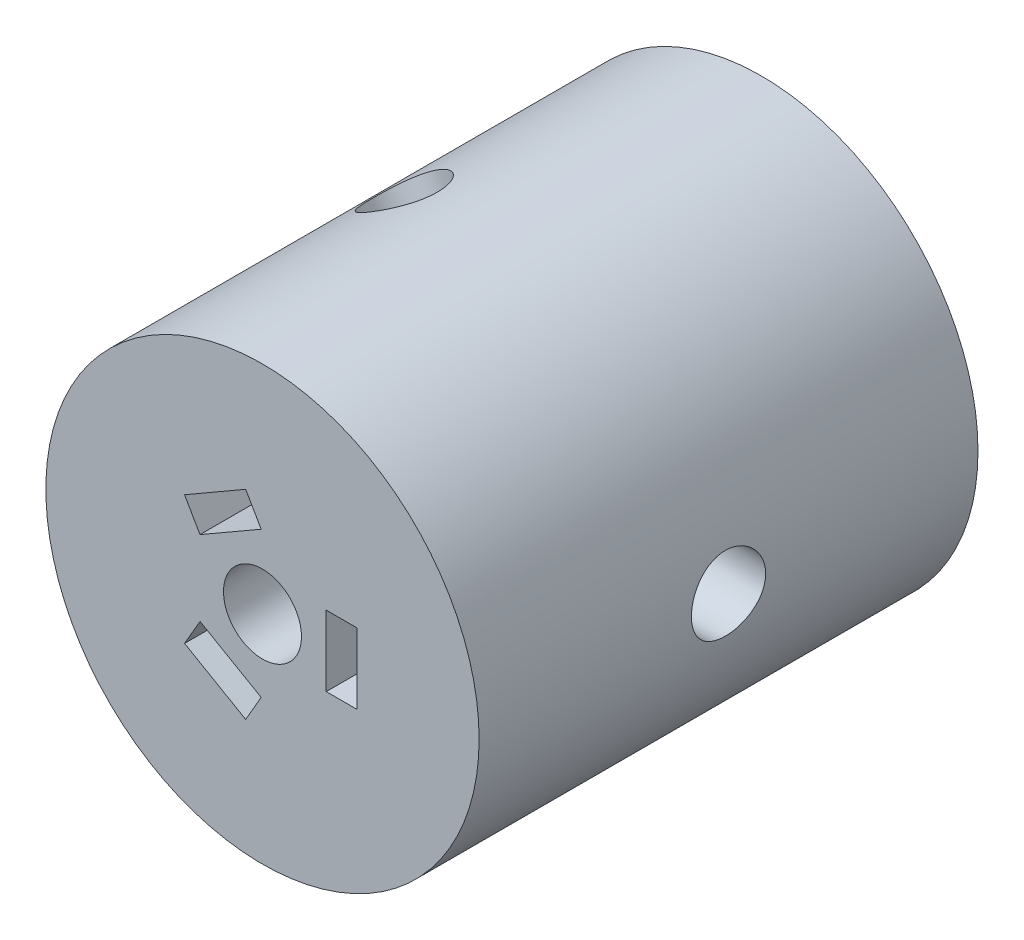
SolidWorks part; units mm, degrees
ref_plane "Front" through (0, 0, 0) normal (0, 0, 1) x (1, 0, 0)
ref_plane "Top" through (0, 0, 0) normal (0, 1, 0) x (1, 0, 0)
ref_plane "Right" through (0, 0, 0) normal (1, 0, 0) x (0, 0, -1)
sketch "Sketch1" plane through (0, 0, 0) normal (0, 0, 1) x (1, 0, 0)
  circle A0 centre (0, 0) radius 17.5
  circle A1 centre (0, 0) radius 3.15
  dimension "D1" = 35
  dimension "D2" = 6.3
extrude "Boss-Extrude1" add sketch "Sketch1" along normal blind 40.3
sketch "Sketch2" plane through (0, 0, 40.3) normal (0, 0, 1) x (1, 0, 0)
  line L3 (7.65, 0) -> (7.65, 2.85)
  line L5 (7.65, 0) -> (7.65, -2.85)
  line L7 (7.65, 2.85) -> (5.15, 2.85)
  line L8 (5.15, 2.85) -> (5.15, -2.85)
  line L9 (5.15, -2.85) -> (7.65, -2.85)
  line L16 (-3.825, -6.6251) -> (-1.3568, -8.0501)
  line L17 (-3.825, -6.6251) -> (-6.2932, -5.2001)
  line L18 (-1.3568, -8.0501) -> (-0.1068, -5.885)
  line L19 (-0.1068, -5.885) -> (-5.0432, -3.035)
  line L20 (-5.0432, -3.035) -> (-6.2932, -5.2001)
  line L21 (-3.825, 6.6251) -> (-6.2932, 5.2001)
  line L22 (-3.825, 6.6251) -> (-1.3568, 8.0501)
  line L23 (-1.3568, 8.0501) -> (-0.1054, 5.8826)
  line L24 (-0.1054, 5.8826) -> (-5.0482, 3.0353)
  line L25 (-5.0482, 3.0353) -> (-6.2932, 5.2001)
  dimension "D5" = 2.85
  dimension "D6" = 2.85
  dimension "D7" = 2.85
  dimension "D8" = 2.85
  dimension "D9" = 2.5
  dimension "D10" = 5.7
  dimension "D11" = 2.85
extrude "Cut-Extrude1" cut sketch "Sketch2" against normal blind 23 contours L9 L5 L3 L7 L8 | L25 L21 L22 L23 L24 | L20 L17 L16 L18 L19
ref_plane "Plane1" through (-8.75, -15.1554, 0) normal (-0.5, -0.866, 0) x (0, 0, -1)
sketch "Sketch8" plane through (-8.75, -15.1554, 0) normal (-0.5, -0.866, 0) x (0, 0, -1)
  circle A0 centre (-20.15, 0) radius 1.65
  dimension "D1" = 3.3
extrude "Cut-Extrude4" cut sketch "Sketch8" against normal up to next
sketch "Sketch10" plane through (-8.75, -15.1554, 0) normal (-0.5, -0.866, 0) x (0, 0, -1)
  circle A0 centre (-20.15, 0) radius 1.65
extrude "Cut-Extrude5" cut sketch "Sketch10" against normal up to next
sketch "Sketch12" plane through (-8.75, -15.1554, 0) normal (-0.5, -0.866, 0) x (0, 0, -1)
  circle A0 centre (-20.15, 0) radius 3
  dimension "D1" = 6
extrude "Cut-Extrude6" cut sketch "Sketch12" against normal blind 5.35
ref_plane "Plane2" through (-8.75, 15.1554, 0) normal (-0.5, 0.866, 0) x (0, 0, -1)
sketch "Sketch15" plane through (-8.75, 15.1554, 0) normal (-0.5, 0.866, 0) x (0, 0, -1)
  circle A0 centre (-20.15, 0) radius 3
extrude "Cut-Extrude8" cut sketch "Sketch15" against normal blind 5.35
sketch "Sketch17" plane through (-8.75, 15.1554, 0) normal (-0.5, 0.866, 0) x (0, 0, -1)
  circle A0 centre (-20.15, 0) radius 1.65
  dimension "D1" = 3.3
extrude "Cut-Extrude9" cut sketch "Sketch17" against normal up to next
sketch "Sketch18" plane through (-8.75, 15.1554, 0) normal (-0.5, 0.866, 0) x (0, 0, -1)
  circle A0 centre (-20.15, 0) radius 1.65
extrude "Cut-Extrude10" cut sketch "Sketch18" against normal up to next
ref_plane "Plane3" through (17.5, 0, 0) normal (1, 0, 0) x (0, 0, -1)
sketch "Sketch19" plane through (17.5, 0, 0) normal (1, 0, 0) x (0, 0, -1)
  circle A0 centre (-20.15, 0) radius 3
extrude "Cut-Extrude11" cut sketch "Sketch19" against normal blind 5.35 contours A0
sketch "Sketch20" plane through (17.5, 0, 0) normal (1, 0, 0) x (0, 0, -1)
  circle A0 centre (-20.15, 0) radius 1.65
  dimension "D1" = 3.3
extrude "Cut-Extrude12" cut sketch "Sketch20" against normal up to next
sketch "Sketch21" plane through (17.5, 0, 0) normal (1, 0, 0) x (0, 0, -1)
  circle A0 centre (-20.15, 0) radius 1.65
extrude "Cut-Extrude13" cut sketch "Sketch21" against normal up to next
